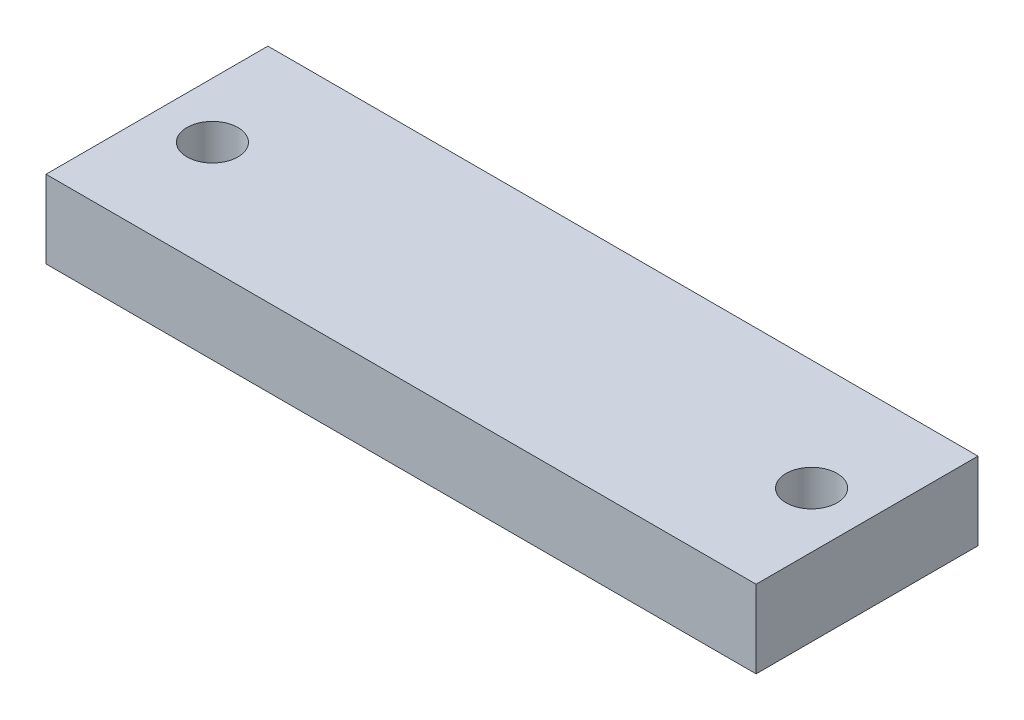
SolidWorks part; units mm, degrees
ref_plane "Front Plane" through (0, 0, 0) normal (0, 0, 1) x (1, 0, 0)
ref_plane "Top Plane" through (0, 0, 0) normal (0, 1, 0) x (1, 0, 0)
ref_plane "Right Plane" through (0, 0, 0) normal (1, 0, 0) x (0, 0, -1)
sketch "Sketch1" plane through (0, 0, 0) normal (0, 1, 0) x (1, 0, 0)
  line L0 (5, 10) -> (59, 10)
  line L1 (0, 0) -> (64, 0)
  line L2 (0, 0) -> (0, 20)
  line L3 (0, 20) -> (64, 20)
  line L4 (64, 0) -> (64, 20)
  circle A0 centre (59, 10) radius 2.3
  circle A1 centre (5, 10) radius 2.3
  point P8 (32, 10)
  point P10 (32, 0)
  point P11 (0, 0)
  point P12 (32, 11.8862)
  point P13 (0, 10)
  dimension "D1" = 4.6
  dimension "D2" = 20
  dimension "D3" = 64
  dimension "D4" = 54
extrude "Boss-Extrude1" add sketch "Sketch1" along normal blind 7
